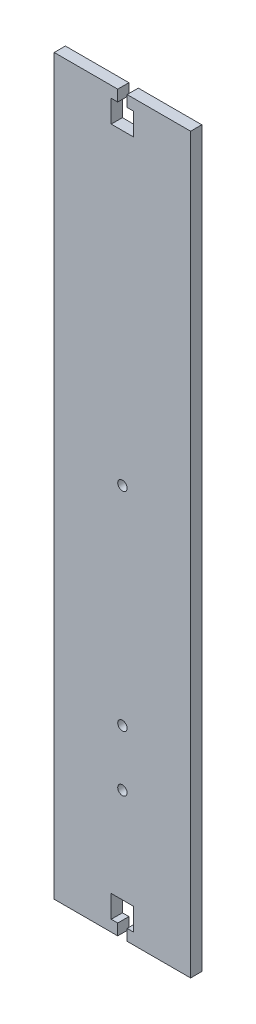
SolidWorks part; units mm, degrees
ref_plane "Front Plane" through (0, 0, 0) normal (0, 0, 1) x (1, 0, 0)
ref_plane "Top Plane" through (0, 0, 0) normal (0, 1, 0) x (1, 0, 0)
ref_plane "Right Plane" through (0, 0, 0) normal (1, 0, 0) x (0, 0, -1)
sketch "Sketch1" plane through (0, 0, 0) normal (0, 0, 1) x (1, 0, 0)
  line L1 (30.505, -164) -> (-30.505, -164)
  line L2 (30.505, -164) -> (30.505, 164)
  line L3 (30.505, 164) -> (-30.505, 164)
  line L4 (-30.505, -164) -> (-30.505, 164)
  line L5 (30.505, -164) -> (-30.505, 164) construction
  line L6 (30.505, 164) -> (-30.505, -164) construction
  point P0 (0, 0)
  dimension "D1" = 328
  dimension "D2" = 61.01
extrude "Boss-Extrude1" add sketch "Sketch1" along normal blind 5
sketch "Sketch2" plane through (0, 0, 5) normal (0, 0, 1) x (1, 0, 0)
  line L2 (30.505, -164) -> (30.505, 164) construction
  line L3 (30.505, -81.5) -> (-30.505, -81.5) construction
  line L4 (-30.505, 164) -> (-30.505, -164) construction
  circle A0 centre (0, -81.5) radius 2.1
  dimension "D1" = 4.2
extrude "Cut-Extrude1" cut sketch "Sketch2" against normal blind 10
sketch "Sketch3" plane through (0, 0, 5) normal (0, 0, 1) x (1, 0, 0)
  line L0 (0, -164) -> (0, -140.2994) construction
  line L1 (-30.505, -164) -> (30.505, -164) construction
  line L2 (-30.505, 0) -> (-12.0598, 0) construction
  line L3 (-30.505, 164) -> (-30.505, -164) construction
  line L4 (-2.1, -164) -> (-2.1, -159)
  line L5 (-2.1, -159) -> (-5, -159)
  line L6 (-5, -159) -> (-5, -149)
  line L7 (-5, -149) -> (5, -149)
  line L8 (-2.1, -164) -> (2.1, -164)
  line L9 (5, -159) -> (5, -149)
  line L10 (2.1, -159) -> (5, -159)
  line L11 (2.1, -164) -> (2.1, -159)
  line L12 (0, 164) -> (0, 140.2994) construction
  line L13 (2.1, 164) -> (2.1, 159)
  line L14 (2.1, 159) -> (5, 159)
  line L15 (5, 159) -> (5, 149)
  line L16 (-2.1, 164) -> (2.1, 164)
  line L17 (-5, 149) -> (5, 149)
  line L18 (-5, 159) -> (-5, 149)
  line L19 (-2.1, 159) -> (-5, 159)
  line L20 (-2.1, 164) -> (-2.1, 159)
  point P16 (0, -149)
  point P28 (0, 149)
  dimension "D1" = 2.1
  dimension "D2" = 5
  dimension "D3" = 10
  dimension "D4" = 5
extrude "Cut-Extrude2" cut sketch "Sketch3" against normal blind 10
sketch "Sketch4" plane through (0, 0, 5) normal (0, 0, 1) x (1, 0, 0)
  line L2 (30.505, -164) -> (30.505, 164) construction
  line L3 (30.505, -106.5) -> (-30.505, -106.5) construction
  line L4 (-30.505, 164) -> (-30.505, -164) construction
  circle A0 centre (0, -106.5) radius 2.1
  dimension "D1" = 4.2
extrude "Cut-Extrude3" cut sketch "Sketch4" against normal blind 5
sketch "Sketch5" plane through (0, 0, 5) normal (0, 0, 1) x (1, 0, 0)
  line L2 (30.505, -164) -> (30.505, 164) construction
  line L3 (30.505, 11.5) -> (-30.505, 11.5) construction
  line L4 (-30.505, 164) -> (-30.505, -164) construction
  circle A0 centre (0, 11.5) radius 2.1
  dimension "D1" = 4.2
extrude "Cut-Extrude4" cut sketch "Sketch5" against normal blind 5
